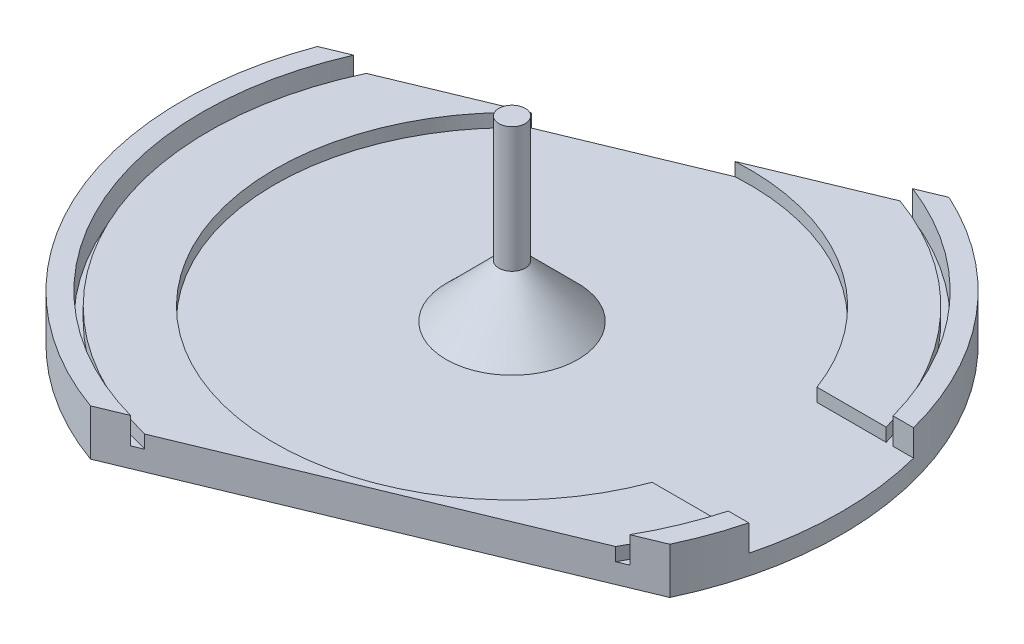
SolidWorks part; units mm, degrees
ref_plane "Front Plane" through (0, 0, 0) normal (0, 0, 1) x (1, 0, 0)
ref_plane "Top Plane" through (0, 0, 0) normal (0, 1, 0) x (1, 0, 0)
ref_plane "Right Plane" through (0, 0, 0) normal (1, 0, 0) x (0, 0, -1)
sketch "Sketch1" plane through (0, 0, 0) normal (0, 1, 0) x (1, 0, 0)
  circle A0 centre (0, 0) radius 50
  dimension "D1" = 100
extrude "Boss-Extrude1" add sketch "Sketch1" along normal blind 3
sketch "Sketch2" plane through (0, 3, 0) normal (0, 1, 0) x (1, 0, 0)
  circle A0 centre (0, 0) radius 47
  circle A1 centre (0, 0) radius 50
  circle A2 centre (0, 0) radius 50
  dimension "D1" = 0
  dimension "D2" = 3
extrude "Boss-Extrude2" add sketch "Sketch2" along normal blind 4
sketch "Sketch3" plane through (0, 3, 0) normal (0, 1, 0) x (1, 0, 0)
  circle A0 centre (0, 0) radius 2
  dimension "D1" = 4
extrude "Boss-Extrude3" add sketch "Sketch3" along normal blind 27
chamfer "Chamfer1" distance 8 angle 45 1 edges at (0, 3, 2)
sketch "Sketch4" plane through (0, 3, 0) normal (0, 1, 0) x (1, 0, 0)
  circle A0 centre (0, 0) radius 36
  circle A1 centre (0, 0) radius 46
  dimension "D1" = 72
  dimension "D2" = 10
extrude "Boss-Extrude4" add sketch "Sketch4" along normal blind 2
sketch "Sketch5" plane through (0, 0, 0) normal (1, 0, 0) x (0, 0, -1)
  line L0 (47, 7) -> (-47, 7) construction
  line L1 (12.5, 3) -> (-12.5, 3)
  line L2 (12.5, 3) -> (12.5, 11)
  line L3 (12.5, 11) -> (-12.5, 11)
  line L4 (-12.5, 3) -> (-12.5, 11)
  line L5 (12.5, 3) -> (-12.5, 11) construction
  line L6 (12.5, 11) -> (-12.5, 3) construction
  point P0 (0, 7)
  dimension "D1" = 25
  dimension "D2" = 8
extrude "Cut-Extrude1" cut sketch "Sketch5" against normal blind 59 from offset 80
sketch "Sketch6" plane through (0, 30, 0) normal (0, 1, 0) x (1, 0, 0)
  line L1 (38.5, -72.7084) -> (-38.5, -72.7084)
  line L2 (38.5, -72.7084) -> (38.5, 72.7084)
  line L3 (38.5, 72.7084) -> (-38.5, 72.7084)
  line L4 (-38.5, -72.7084) -> (-38.5, 72.7084)
  line L5 (38.5, -72.7084) -> (-38.5, 72.7084) construction
  line L6 (38.5, 72.7084) -> (-38.5, -72.7084) construction
  point P0 (0, 0)
  dimension "D1" = 77
sketch "Sketch7" plane through (0, 0, 0) normal (0, -1, 0) x (1, 0, 0)
  line L4 (94.7924, -104.2624) -> (96.3246, -100.5675)
  line L5 (-159.2328, 1.076) -> (94.7924, -104.2624)
  line L6 (-157.7006, 4.771) -> (-159.2328, 1.076)
  line L7 (96.3246, -100.5675) -> (-157.7006, 4.771)
  line L8 (94.7924, -104.2624) -> (96.3246, -100.5675)
  line L9 (-159.2328, 1.076) -> (94.7924, -104.2624)
  line L10 (-157.7006, 4.771) -> (-159.2328, 1.076)
  line L11 (96.3246, -100.5675) -> (-157.7006, 4.771)
  line L12 (133.0973, -11.8896) -> (134.6295, -8.1947)
  line L13 (-120.9279, 93.4488) -> (133.0973, -11.8896)
  line L14 (-119.3957, 97.1438) -> (-120.9279, 93.4488)
  line L15 (134.6295, -8.1947) -> (-119.3957, 97.1438)
  line L16 (133.0973, -11.8896) -> (134.6295, -8.1947)
  line L17 (-120.9279, 93.4488) -> (133.0973, -11.8896)
  line L18 (-119.3957, 97.1438) -> (-120.9279, 93.4488)
  line L19 (134.6295, -8.1947) -> (-119.3957, 97.1438)
  line L20 (87.8444, -76.4822) -> (86.6953, -79.2534)
  line L21 (93.3868, -78.7805) -> (87.8444, -76.4822)
  line L22 (92.2377, -81.5516) -> (93.3868, -78.7805)
  line L23 (86.6953, -79.2534) -> (92.2377, -81.5516)
  line L24 (87.8444, -76.4822) -> (86.6953, -79.2534)
  line L25 (93.3868, -78.7805) -> (87.8444, -76.4822)
  line L26 (92.2377, -81.5516) -> (93.3868, -78.7805)
  line L27 (86.6953, -79.2534) -> (92.2377, -81.5516)
  line L156 (92.2377, -81.5516) -> (93.3868, -78.7805)
  line L157 (92.2377, -81.5516) -> (86.6953, -79.2534)
  line L158 (93.3868, -78.7805) -> (-140.1724, 18.0712)
  line L159 (-142.2485, 13.0645) -> (-140.1724, 18.0712)
  line L160 (133.0973, -11.8896) -> (-120.9279, 93.4488)
  line L161 (133.0973, -11.8896) -> (149.8477, 28.5044)
  line L162 (-120.9279, 93.4488) -> (-104.1775, 133.8428)
  line L163 (149.8477, 28.5044) -> (-104.1775, 133.8428)
  line L164 (93.3868, -78.7805) -> (80.7485, -103.3475)
  line L165 (80.7485, -103.3475) -> (-142.2485, 11.3718)
  line L166 (-142.2485, 11.3718) -> (-142.2485, 13.0645)
  circle A1 centre (0, 0) radius 50
  circle A2 centre (0, 0) radius 50
  point P14 (86.6953, -91.7878)
  point P22 (0, 0)
  dimension "D1" = 0
  dimension "D2" = 0
  dimension "D3" = 0
  dimension "D4" = 0
extrude "Cut-Extrude2" cut sketch "Sketch7" against normal blind 10
sketch "Sketch8" plane through (0, 0, 0) normal (0, -1, 0) x (1, 0, 0)
  line L0 (41.8847, 22.6865) -> (-13.539, 45.6694)
  line L1 (-44.089, -18.5247) -> (18.0416, -44.2888)
  line L2 (-45.2381, -21.2959) -> (16.8925, -47.06)
  line L3 (43.0338, 25.4577) -> (-12.3899, 48.4406)
  line L4 (-45.2381, -21.2959) -> (16.8925, -47.06)
  line L5 (43.0338, 25.4577) -> (-12.3899, 48.4406)
  line L6 (18.0416, -44.2888) -> (23.8769, -46.7086)
  line L7 (23.8769, -46.7086) -> (16.8925, -47.06)
  line L8 (-44.089, -18.5247) -> (-49.6446, -16.2209)
  line L9 (-49.6446, -16.2209) -> (-45.2381, -21.2959)
  line L10 (-11.39, 44.7783) -> (-22.3334, 49.3162)
  line L11 (-22.3334, 49.3162) -> (-12.3899, 48.4406)
  line L12 (41.3872, 22.8928) -> (46.2805, 20.8636)
  line L13 (46.2805, 20.8636) -> (43.0338, 25.4577)
  arc A2 (-12.3899, 48.4406) -> (-45.2381, -21.2959) centre (0, 0) ccw
  arc A3 (16.8925, -47.06) -> (43.0338, 25.4577) centre (0, 0) ccw
  arc M5 (-12.3899, 48.4406) -> (-45.2381, -21.2959) centre (0, 0) ccw
  line M6 (-45.2381, -21.2959) -> (16.8925, -47.06)
  arc M7 (16.8925, -47.06) -> (43.0338, 25.4577) centre (0, 0) ccw
  line M8 (43.0338, 25.4577) -> (-12.3899, 48.4406)
  dimension "D1" = 0
  dimension "D2" = 3
extrude "Cut-Extrude3" cut sketch "Sketch8" against normal blind 10 contours L1 L8 L6 M5 M6 M7 | L0 L12 L10 M7 M8 M5
